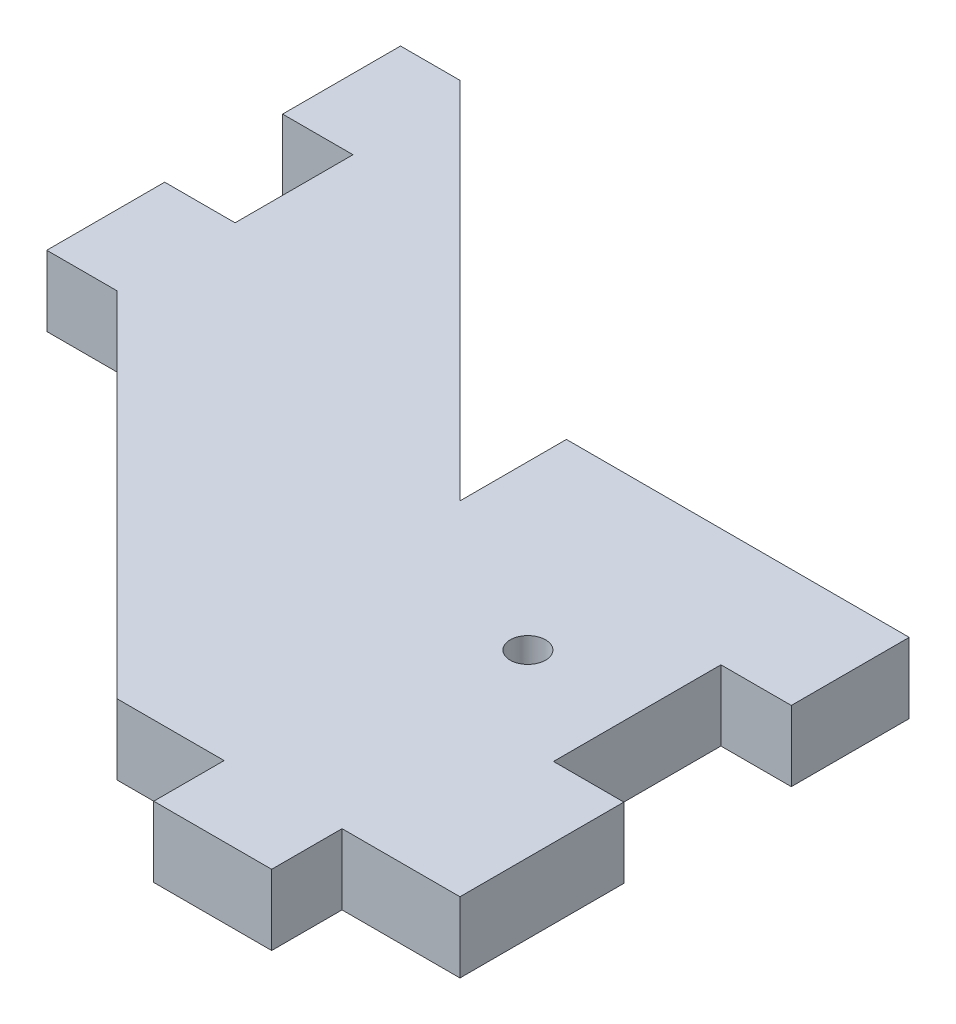
SolidWorks part; units mm, degrees
ref_plane "Front Plane" through (0, 0, 0) normal (0, 0, 1) x (1, 0, 0)
ref_plane "Top Plane" through (0, 0, 0) normal (0, 1, 0) x (1, 0, 0)
ref_plane "Right Plane" through (0, 0, 0) normal (1, 0, 0) x (0, 0, -1)
sketch "Sketch1" plane through (0, 0, 0) normal (0, 1, 0) x (1, 0, 0)
  line L0 (0, 0) -> (-5.969, 0)
  line L1 (-5.969, 0) -> (-5.969, 10)
  line L2 (-5.969, 10) -> (0, 10)
  line L3 (0, 10) -> (0, 20)
  line L4 (0, 20) -> (-5.969, 20)
  line L5 (-5.969, 20) -> (-5.969, 30)
  line L6 (-5.969, 30) -> (-0.928, 30)
  line L7 (-0.928, 30) -> (59.031, -29.959)
  line L8 (59.031, -29.959) -> (49.031, -29.959)
  line L9 (49.031, -29.959) -> (49.031, -35.928)
  line L10 (49.031, -35.928) -> (39.031, -35.928)
  line L11 (39.031, -35.928) -> (39.031, -29.959)
  line L12 (39.031, -29.959) -> (29.959, -29.959)
  line L13 (29.959, -29.959) -> (0, 0)
  dimension "D1" = 5.969
  dimension "D2" = 10
  dimension "D3" = 65
  dimension "D4" = 10
  dimension "D5" = 65.928
  dimension "D6" = 135
extrude "Boss-Extrude1" add sketch "Sketch1" along normal blind 5.969
sketch "Sketch2" plane through (0, 5.969, 0) normal (0, 1, 0) x (1, 0, 0)
  line L1 (59.031, -29.959) -> (29.959, -29.959)
  line L2 (59.031, -29.959) -> (59.031, -16.059)
  line L3 (59.031, 8.141) -> (29.959, 8.141)
  line L4 (29.959, -29.959) -> (29.959, 8.141)
  line L6 (59.031, -1.859) -> (59.031, 8.141)
  line L7 (59.031, -16.059) -> (53.062, -16.059)
  line L9 (59.031, -1.859) -> (53.062, -1.859)
  line L10 (53.062, -16.059) -> (53.062, -1.859)
  circle A1 centre (43.791, -8.959) radius 1.5
  dimension "D3" = 15.24
  dimension "D7" = 3
  dimension "D1" = 21
  dimension "D2" = 38.1
  dimension "D4" = 5.969
  dimension "D5" = 10
  dimension "D6" = 14.2
extrude "Boss-Extrude2" add sketch "Sketch2" against normal up to surface (5.969 mm away) up to face at (17.165, 0, 5.1209)
